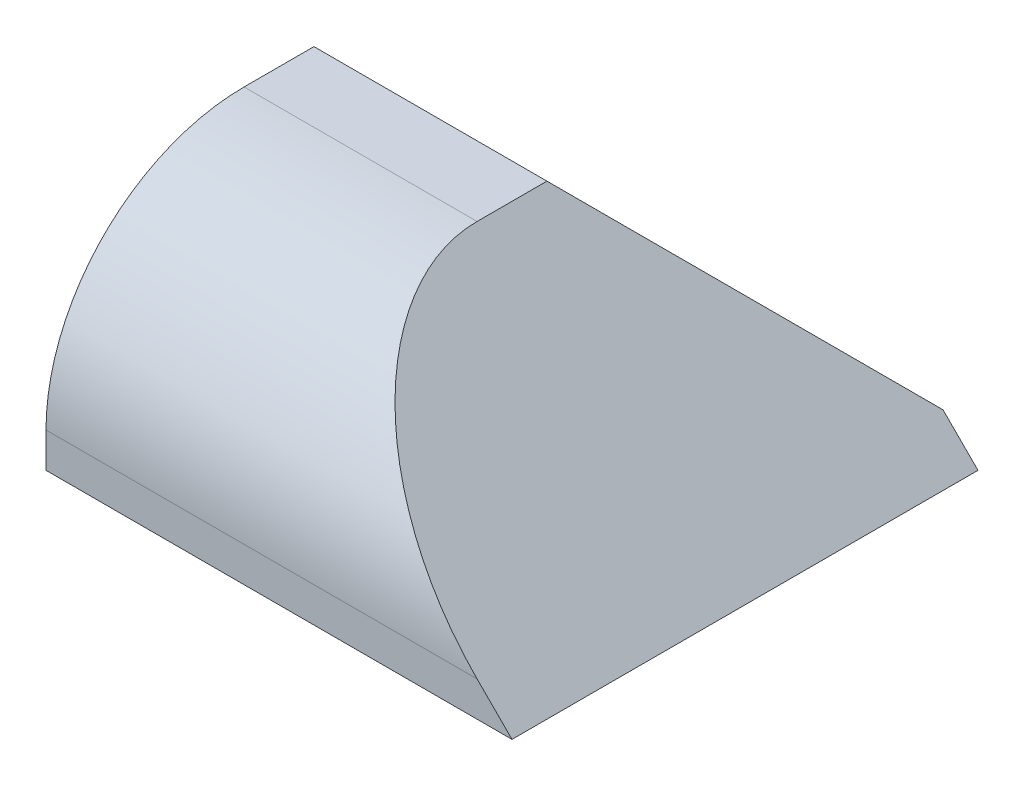
SolidWorks part; units mm, degrees
ref_plane "Front Plane" through (0, 0, 0) normal (0, 0, 1) x (1, 0, 0)
ref_plane "Top Plane" through (0, 0, 0) normal (0, 1, 0) x (1, 0, 0)
ref_plane "Right Plane" through (0, 0, 0) normal (1, 0, 0) x (0, 0, -1)
sketch "Sketch1" plane through (0, 0, 0) normal (0, 1, 0) x (1, 0, 0)
  line L1 (0, 0) -> (20, 0)
  line L2 (0, 0) -> (0, 20)
  line L3 (0, 20) -> (20, 20)
  line L4 (20, 0) -> (20, 20)
  dimension "D1" = 20
  dimension "D2" = 20
extrude "Boss-Extrude1" add sketch "Sketch1" along normal blind 10
sketch "Sketch2" plane through (20, 0, 0) normal (1, 0, 0) x (0, 0, -1)
  line L0 (20, 1.5) -> (11.5, 10)
  line L1 (20, 10) -> (20, 0) construction
  line L2 (0, 10) -> (20, 10) construction
  line L3 (0, 10) -> (0, 0) construction
  line L4 (0, 1.5) -> (0, 10)
  line L5 (0, 10) -> (8.5, 10)
  line L6 (11.5, 10) -> (20, 10)
  line L7 (20, 10) -> (20, 1.5)
  arc A0 (0, 1.5) -> (8.5, 10) centre (8.5, 1.5) cw
  dimension "D1" = 45
  dimension "D2" = 1.5
  dimension "D3" = 1.5
extrude "Cut-Extrude1" cut sketch "Sketch2" against normal through all
sketch "Sketch3" plane through (0, 0, -20) normal (0, 0, -1) x (-1, 0, 0)
  line L0 (-20, 0) -> (-10, 10)
  line L1 (-10, 10) -> (-20, 10)
  line L2 (-20, 10) -> (-20, 0)
  dimension "D1" = 45
extrude "Cut-Extrude2" cut sketch "Sketch3" against normal through all
